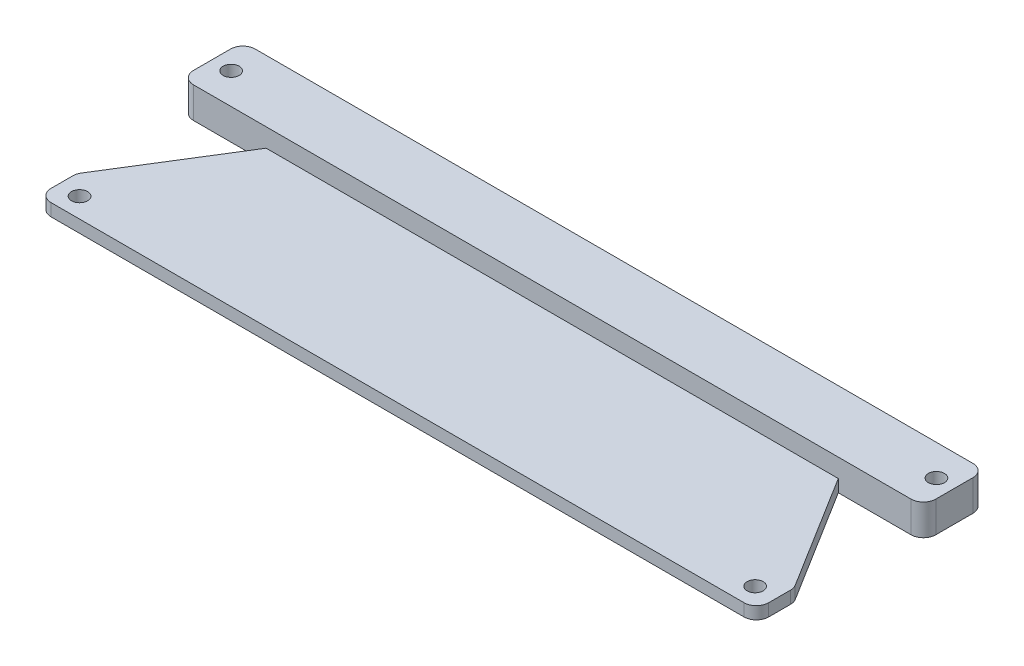
SolidWorks part; units mm, degrees
ref_plane "Front Plane" through (0, 0, 0) normal (0, 0, 1) x (1, 0, 0)
ref_plane "Top Plane" through (0, 0, 0) normal (0, 1, 0) x (1, 0, 0)
ref_plane "Right Plane" through (0, 0, 0) normal (1, 0, 0) x (0, 0, -1)
sketch "Sketch1" plane through (0, 0, 0) normal (0, 1, 0) x (1, 0, 0)
  line L0 (-76.2, 0) -> (76.2, 0)
  point P4 (0, 0)
extrude "Extrude-Thin1" add sketch "Sketch1" along normal blind 6.35 thin
fillet "Fillet1" radius 2.54 4 edges at (76.2, 3.175, 12.7) (76.2, 3.175, 0) (-76.2, 3.175, 12.7) (-76.2, 3.175, 0)
sketch "Sketch3" plane through (0, 6.35, 0) normal (0, 1, 0) x (1, 0, 0)
  circle A0 centre (72.5201, -6.35) radius 1.651
extrude "Cut-Extrude1" cut sketch "Sketch3" against normal blind 6.35
pattern_linear "LPattern1" count 2 spacing 144.78 along (-1, 0, 0) of "Cut-Extrude1"
sketch "Sketch4" plane through (0, 0, 12.7) normal (0, 0, 1) x (1, 0, 0)
  line L0 (-73.66, 0) -> (73.66, 0)
extrude "Extrude-Thin2" add sketch "Sketch4" along direction (0, 0, -1) on the side of the normal blind 31.75 thin thin type one direction reverse wall 2.54
sketch "Sketch5" plane through (0, 0, 0) normal (0, -1, 0) x (-1, 0, 0)
  line L0 (-73.66, -12.7) -> (-58.7274, -12.7)
  line L2 (-73.66, -44.45) -> (-73.66, -12.7) construction
  line L3 (-58.7274, -12.7) -> (-73.66, -36.7046)
  line L4 (-73.66, -12.7) -> (-73.66, -36.7046)
  arc A0 (-76.2, -10.16) -> (-73.66, -12.7) centre (-73.66, -10.16) ccw construction
extrude "Cut-Extrude2" cut sketch "Sketch5" against normal blind 2.54 contours L0 L3 L4
mirror "Mirror1" about plane through (0, 0, 0) normal (1, 0, 0) of "Cut-Extrude2"
fillet "Fillet2" radius 2.54 4 edges at (-73.66, 1.27, 36.7046) (73.66, 1.27, 36.7046) (73.66, 1.27, 44.45) (-73.66, 1.27, 44.45)
sketch "Sketch7" plane through (0, 2.54, 0) normal (0, 1, 0) x (1, 0, 0)
  circle A0 centre (-69.342, -40.386) radius 1.651
extrude "Cut-Extrude3" cut sketch "Sketch7" against normal blind 2.54 contours A0
mirror "Mirror2" about plane through (0, 0, 0) normal (1, 0, 0) of "Cut-Extrude3"
